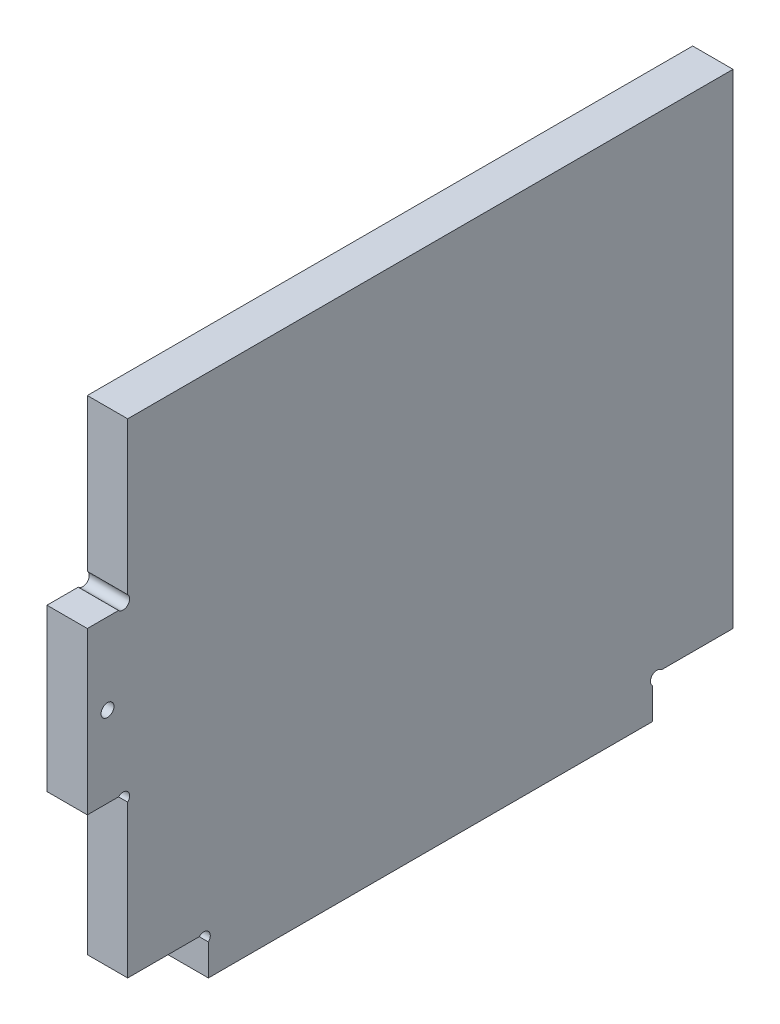
SolidWorks part; units mm, degrees
ref_plane "Plan de face" through (0, 0, 0) normal (0, 0, 1) x (1, 0, 0)
ref_plane "Plan de dessus" through (0, 0, 0) normal (0, 1, 0) x (1, 0, 0)
ref_plane "Plan de droite" through (0, 0, 0) normal (1, 0, 0) x (0, 0, -1)
sketch "Esquisse1" plane through (0, 0, 0) normal (1, 0, 0) x (0, 0, -1)
  line L0 (-9.0454, 0) -> (230.8255, 0) construction
  line L1 (0, -12.497) -> (0, 166.1964) construction
  line L2 (-9.0454, 130) -> (230.8255, 130) construction
  line L3 (160, -24.8739) -> (160, 166.1964) construction
  line L4 (85, 150.9559) -> (85, -7.3756) construction
  line L5 (-9.0454, 10) -> (194.9822, 10) construction
  line L6 (-9.0454, 70) -> (194.9822, 70) construction
  line L7 (10, 150.9559) -> (10, -12.497) construction
  line L8 (140, 14.9206) -> (140, -24.8739) construction
  line L9 (-9.0454, 50) -> (42.2952, 50) construction
  line L10 (10, 50) -> (-22.1554, 17.8446) construction
  line L11 (140, 7.7373) -> (140, 0)
  line L12 (140, 10) -> (157.4309, -7.4309) construction
  line L13 (30, 7.7373) -> (30, 0)
  line L14 (0, 50) -> (7.7373, 50)
  line L15 (0, 90) -> (7.7373, 90)
  line L16 (30, 0) -> (140, 0)
  line L17 (27.7373, 10) -> (10, 10)
  line L18 (10, 10) -> (10, 47.7373)
  line L19 (0, 50) -> (0, 90)
  line L20 (10, 92.2627) -> (10, 130)
  line L21 (10, 130) -> (160, 130)
  line L22 (160, 130) -> (160, 10)
  line L23 (160, 10) -> (142.2627, 10)
  arc A0 (142.2627, 10) -> (140, 7.7373) centre (141.1314, 8.8686) ccw
  arc A1 (10, 47.7373) -> (7.7373, 50) centre (8.8686, 48.8686) ccw
  arc A2 (27.7373, 10) -> (30, 7.7373) centre (28.8686, 8.8686) cw
  arc A3 (10, 92.2627) -> (7.7373, 90) centre (8.8686, 91.1314) cw
  circle A4 centre (5, 70) radius 1.6
  dimension "D1" = 160
  dimension "D2" = 130
  dimension "D3" = 60
  dimension "D4" = 10
  dimension "D5" = 10
  dimension "D6" = 75
  dimension "D7" = 20
  dimension "D8" = 20
  dimension "D9" = 45
  dimension "D10" = 45
extrude "Extrusion1" add sketch "Esquisse1" along normal blind 10
